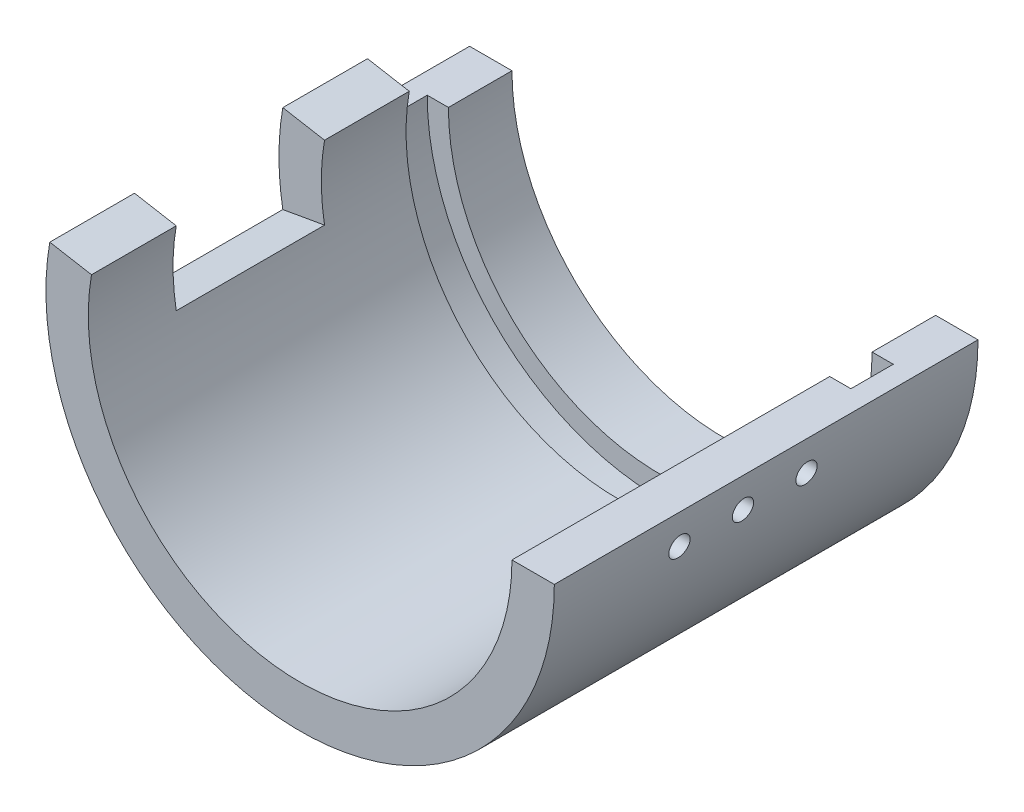
SolidWorks part; units mm, degrees
ref_plane "Front Plane" through (0, 0, 0) normal (0, 0, 1) x (1, 0, 0)
ref_plane "Top Plane" through (0, 0, 0) normal (0, 1, 0) x (1, 0, 0)
ref_plane "Right Plane" through (0, 0, 0) normal (1, 0, 0) x (0, 0, -1)
sketch "Sketch1" plane through (0, 0, 0) normal (0, 1, 0) x (1, 0, 0)
  line L0 (0, 69.1176) -> (0, -71.4706) construction
  line L1 (-60, 19.1176) -> (-60, -80.8824)
  line L2 (-60, 19.1176) -> (-50, 19.1176)
  line L3 (-50, 19.1176) -> (-50, 4.1176)
  line L4 (-50, 4.1176) -> (-55, 4.1176)
  line L5 (-55, 4.1176) -> (-55, -5.8824)
  line L6 (-55, -5.8824) -> (-50, -5.8824)
  line L7 (-50, -5.8824) -> (-50, -80.8824)
  line L8 (-50, -80.8824) -> (-60, -80.8824)
  dimension "D1" = 15
  dimension "D2" = 10
  dimension "D3" = 5
  dimension "D4" = 10
  dimension "D5" = 10
  dimension "D6" = 100
  dimension "D7" = 50
revolve "Revolve1" add sketch "Sketch1" angle 180 about L0
ref_plane "Plane1" through (60, 0, 0) normal (1, 0, 0) x (0, 0, 1)
sketch "Sketch2" plane through (0, 0, 0) normal (0, 1, 0) x (1, 0, 0)
  line L0 (-50, -60.8824) -> (-60, -60.8824)
  line L1 (-50, -80.8824) -> (-50, -5.8824) construction
  line L2 (-60, 19.1176) -> (-60, -80.8824) construction
  line L3 (-60, -60.8824) -> (-60, -25.8824)
  line L4 (-60, -25.8824) -> (-50, -25.8824)
  line L5 (-50, -25.8824) -> (-50, -60.8824)
  line L6 (-60, -80.8824) -> (-50, -80.8824) construction
  line L7 (-50, -5.8824) -> (-55, -5.8824) construction
  line L8 (0, -80.8824) -> (0, -5.8824) construction
  line L9 (-50, -80.8824) -> (50, -80.8824) construction
  line L10 (55, -5.8824) -> (-55, -5.8824) construction
  point P10 (-55, -80.8824)
  dimension "D1" = 20
  dimension "D2" = 20
revolve "Cut-Revolve1" cut sketch "Sketch2" angle 10 about L8
sketch "Sketch4" plane through (60, 0, 0) normal (1, 0, 0) x (0, 0, 1)
  line L0 (-55, 0) -> (55, 0) construction
  line L2 (80.8824, 0) -> (80.8824, 50) construction
  circle A0 centre (35.8824, 7.5) radius 2.5
  circle A1 centre (50.8824, 7.5) radius 2.5
  circle A2 centre (20.8824, 7.5) radius 2.5
  dimension "D2" = 5
  dimension "D3" = 5
  dimension "D6" = 5
  dimension "D1" = 7.5
  dimension "D4" = 7.5
  dimension "D5" = 15
  dimension "D7" = 15
  dimension "D8" = 30
extrude "Cut-Extrude1" cut sketch "Sketch4" against normal blind 20
sketch "Sketch5" plane through (0, 0, 0) normal (0, 1, 0) x (1, 0, 0)
  line L0 (-60, -80.8824) -> (-60, -60.8824)
  line L1 (-60, -60.8824) -> (-50, -60.8824)
  line L2 (-50, -60.8824) -> (-50, -80.8824)
  line L3 (-50, -80.8824) -> (-60, -80.8824)
  line L4 (-60, -25.8824) -> (-60, -5.8824)
  line L5 (-60, 19.1176) -> (-60, -25.8824) construction
  line L6 (-60, -5.8824) -> (-50, -5.8824)
  line L7 (-50, -25.8824) -> (-50, -5.8824) construction
  line L8 (-50, -5.8824) -> (-55, -5.8824) construction
  line L9 (-50, -5.8824) -> (-50, -25.8824)
  line L10 (-50, -25.8824) -> (-60, -25.8824)
  line L11 (0, -85.861) -> (0, 12.6161) construction
  line L12 (0, -55) -> (0, 55) construction
revolve "Revolve2" add sketch "Sketch5" angle 10 about L11
